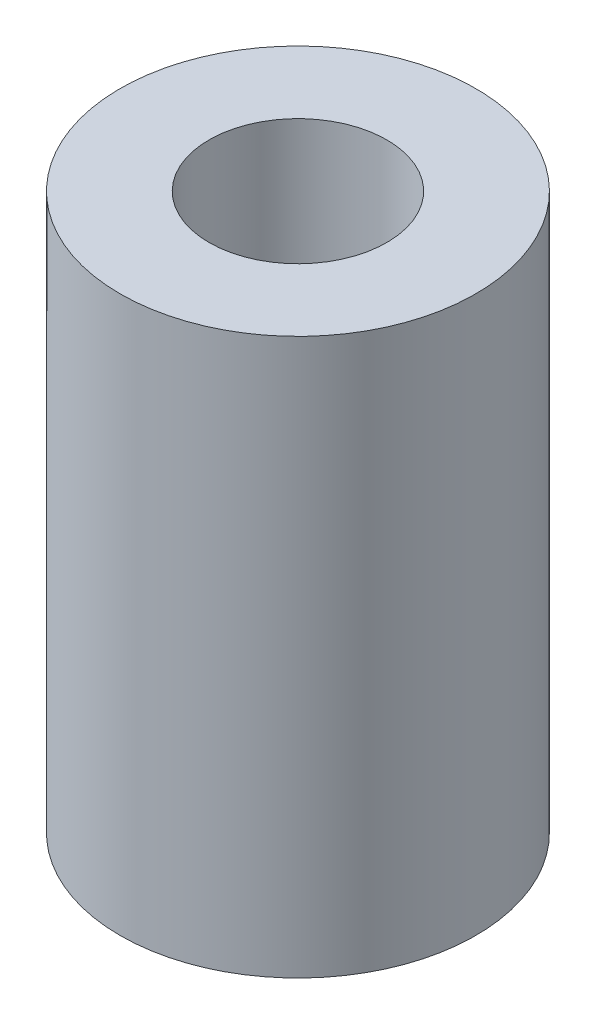
SolidWorks part; units mm, degrees
ref_plane "Front Plane" through (0, 0, 0) normal (0, 0, 1) x (1, 0, 0)
ref_plane "Top Plane" through (0, 0, 0) normal (0, 1, 0) x (1, 0, 0)
ref_plane "Right Plane" through (0, 0, 0) normal (1, 0, 0) x (0, 0, -1)
sketch "Sketch1" plane through (0, 0, 0) normal (0, 1, 0) x (1, 0, 0)
  line L0 (-8.378, 0) -> (8.378, 0) construction
  line L1 (0, 8.4467) -> (0, -8.4467) construction
  circle A0 centre (0, 0) radius 4
  circle A1 centre (0, 0) radius 2
  point P4 (0, 0)
  point P8 (0, 0)
  dimension "D1" = 4
  dimension "D2" = 8
extrude "Boss-Extrude1" add sketch "Sketch1" along normal blind 12.5
